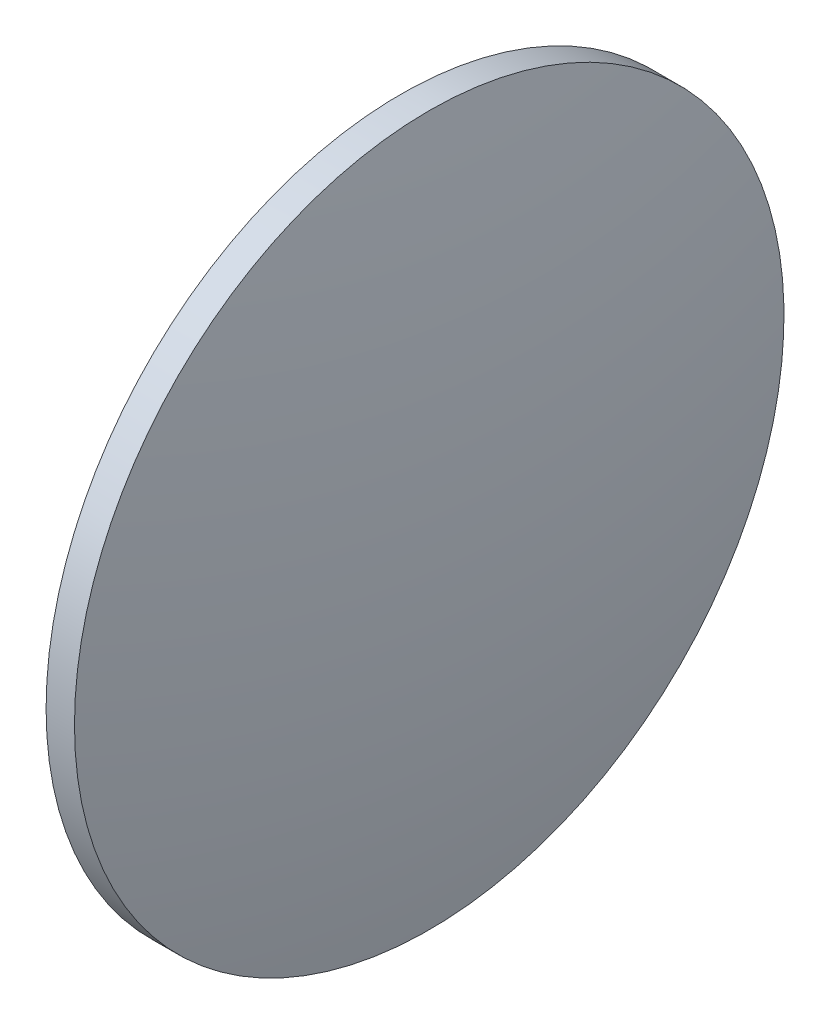
SolidWorks part; units mm, degrees
ref_plane "前视基准面" through (0, 0, 0) normal (0, 0, 1) x (1, 0, 0)
ref_plane "上视基准面" through (0, 0, 0) normal (0, 1, 0) x (1, 0, 0)
ref_plane "右视基准面" through (0, 0, 0) normal (1, 0, 0) x (0, 0, -1)
sketch "草图2" plane through (0, 0, 0) normal (0, 0, 1) x (1, 0, 0)
  line L0 (217.9946, 130.4671) -> (258.5717, 130.4671) construction
  line L1 (225.9713, 130.4671) -> (225.9713, 180.4671)
  line L2 (225.9713, 180.4671) -> (229.9713, 180.4671)
  line L3 (234.8613, 130.4671) -> (225.9713, 130.4671)
  arc A0 (234.8613, 130.4671) -> (229.9713, 180.4671) centre (-23.2074, 130.4671) ccw
revolve "旋转1" add sketch "草图2" angle 360 about L0
